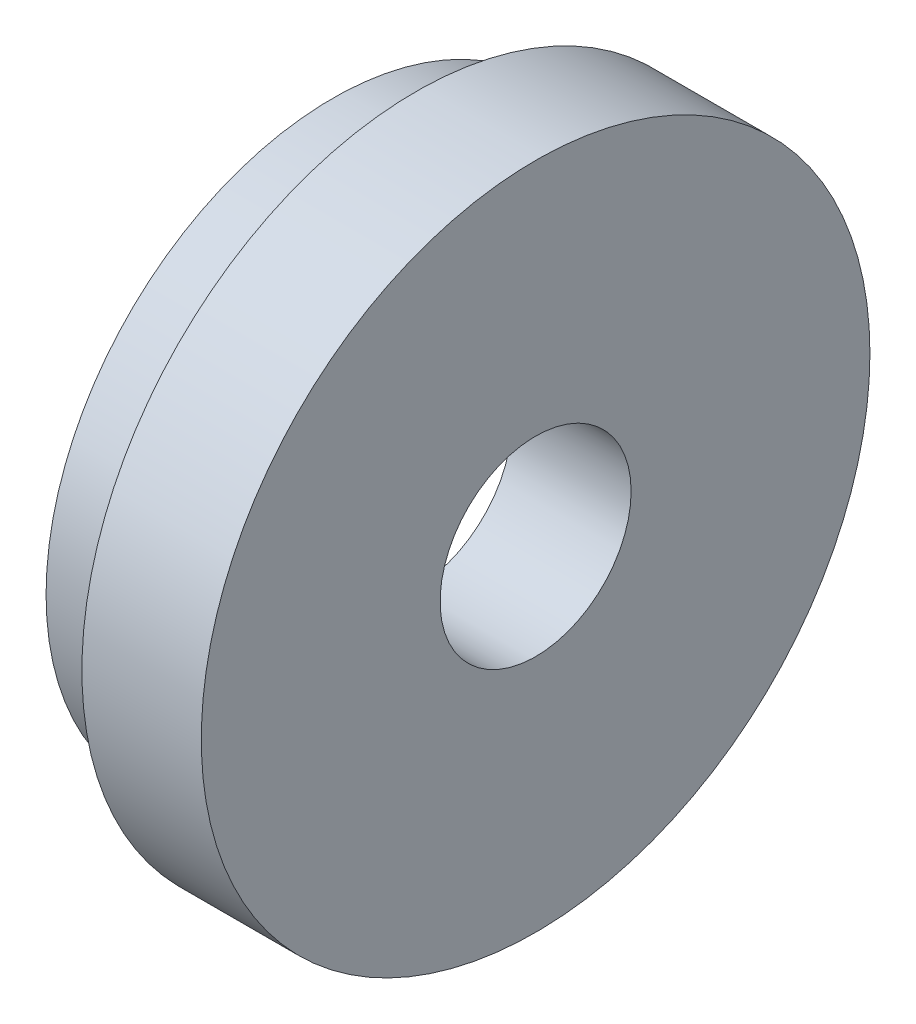
SolidWorks part; units mm, degrees
ref_plane "Alzado" through (0, 0, 0) normal (0, 0, 1) x (1, 0, 0)
ref_plane "Planta" through (0, 0, 0) normal (0, 1, 0) x (1, 0, 0)
ref_plane "Vista lateral" through (0, 0, 0) normal (1, 0, 0) x (0, 0, -1)
sketch "Croquis1" plane through (0, 0, 0) normal (1, 0, 0) x (0, 0, -1)
  circle A0 centre (0, 0) radius 14
  circle A1 centre (0, 0) radius 4
  dimension "D1" = 28
  dimension "D2" = 8
extrude "Saliente-Extruir1" add sketch "Croquis1" along normal blind 5
sketch "Croquis2" plane through (0, 0, 0) normal (-1, 0, 0) x (0, 0, 1)
  circle A0 centre (0, 0) radius 11
  circle A1 centre (0, 0) radius 12
  dimension "D1" = 22
  dimension "D2" = 24
extrude "Saliente-Extruir2" add sketch "Croquis2" along normal blind 3.5
